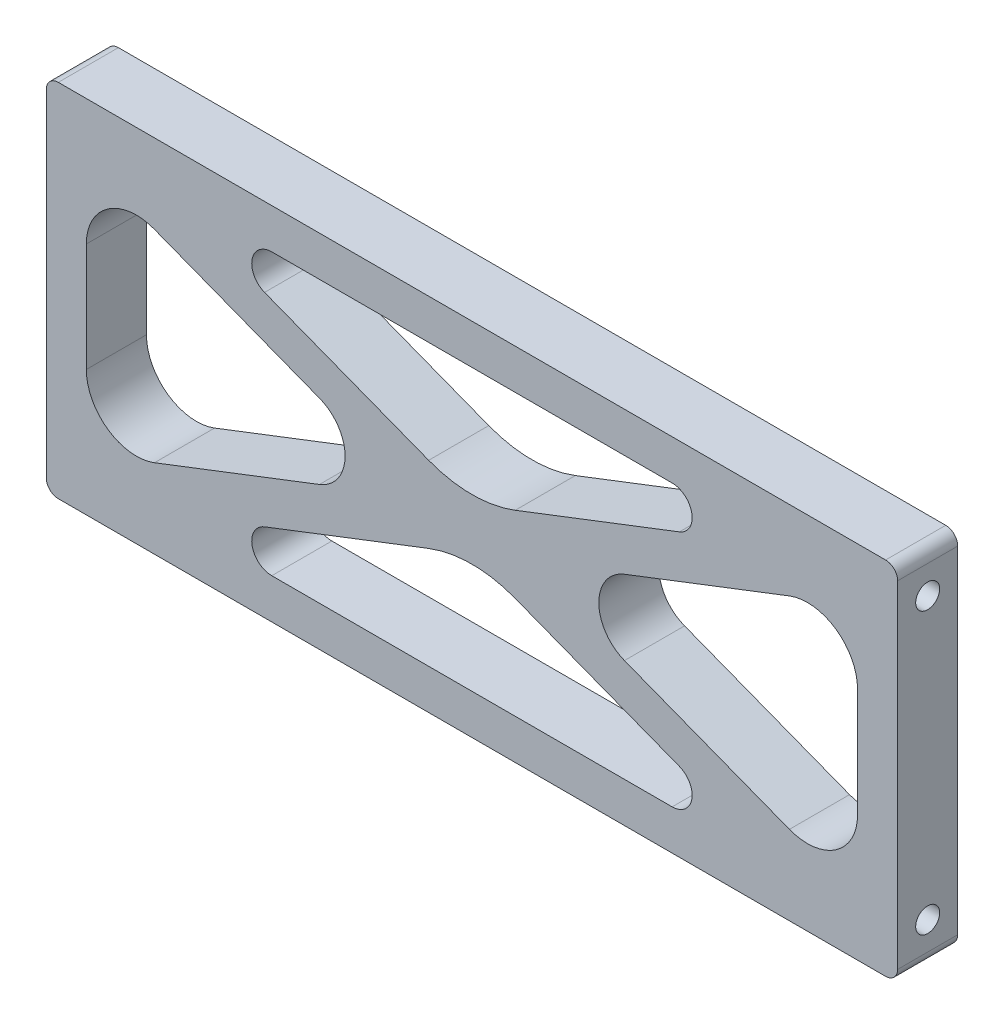
SolidWorks part; units mm, degrees
material "6061-T6 (SS)"
ref_plane "Front" through (0, 0, 0) normal (0, 0, 1) x (1, 0, 0)
ref_plane "Top" through (0, 0, 0) normal (0, 1, 0) x (1, 0, 0)
ref_plane "Right" through (0, 0, 0) normal (1, 0, 0) x (0, 0, -1)
sketch "Sketch1" plane through (0, 0, 0) normal (0, 0, 1) x (1, 0, 0)
  line L1 (-67.4624, 28.575) -> (67.4624, 28.575)
  line L2 (-67.4624, 28.575) -> (-67.4624, -28.575)
  line L3 (-67.4624, -28.575) -> (67.4624, -28.575)
  line L4 (67.4624, 28.575) -> (67.4624, -28.575)
  line L5 (-67.4624, 28.575) -> (67.4624, -28.575) construction
  line L6 (-67.4624, -28.575) -> (67.4624, 28.575) construction
  line L7 (67.4624, -22.225) -> (-67.4624, -22.225) construction
  line L8 (67.4624, -22.225) -> (67.4624, 22.225) construction
  line L9 (67.4624, 22.225) -> (-67.4624, 22.225) construction
  line L10 (-67.4624, -22.225) -> (-67.4624, 22.225) construction
  line L11 (67.4624, -22.225) -> (-67.4624, 22.225) construction
  line L12 (67.4624, 22.225) -> (-67.4624, -22.225) construction
  point P0 (0, 0)
  point P6 (0, 0)
  dimension "D1" = 134.9248
  dimension "D2" = 57.15
  dimension "D3" = 44.45
extrude "Boss-Extrude1" add sketch "Sketch1" along normal mid plane 9.525
sketch "Sketch3" plane through (0, 0, 4.7625) normal (0, 0, 1) x (1, 0, 0)
  line L0 (67.4624, -26.035) -> (-67.4624, 26.035) construction
  line L1 (67.4624, 26.035) -> (-67.4624, -26.035) construction
  line L2 (-61.1124, 8.6099) -> (-61.1124, -8.6099)
  line L3 (-50.3171, -16.0151) -> (-24.1693, -5.9242)
  line L4 (-24.1693, 5.9242) -> (-50.3171, 16.0151)
  line L5 (-31.7257, -22.225) -> (31.7257, -22.225)
  line L6 (32.8688, -16.0879) -> (6.8587, -6.0501)
  line L7 (-6.8587, -6.0501) -> (-32.8688, -16.0879)
  line L8 (-67.4624, 0) -> (67.4624, 0) construction
  line L9 (-67.4624, 28.575) -> (-67.4624, -28.575) construction
  line L10 (67.4624, -28.575) -> (67.4624, 28.575) construction
  line L11 (0, 28.575) -> (0, -28.575) construction
  line L12 (67.4624, 28.575) -> (-67.4624, 28.575) construction
  line L13 (-67.4624, -28.575) -> (67.4624, -28.575) construction
  line L14 (-31.7257, 22.225) -> (31.7257, 22.225)
  line L15 (32.8688, 16.0879) -> (6.8587, 6.0501)
  line L16 (-6.8587, 6.0501) -> (-32.8688, 16.0879)
  line L17 (61.1124, 8.6099) -> (61.1124, -8.6099)
  line L18 (50.3171, -16.0151) -> (24.1693, -5.9242)
  line L19 (24.1693, 5.9242) -> (50.3171, 16.0151)
  arc A0 (-24.1693, -5.9242) -> (-24.1693, 5.9242) centre (-26.4555, 0) ccw
  arc A1 (-61.1124, -8.6099) -> (-50.3171, -16.0151) centre (-53.1749, -8.6099) ccw
  arc A2 (-61.1124, 8.6099) -> (-50.3171, 16.0151) centre (-53.1749, 8.6099) cw
  arc A3 (31.7257, -22.225) -> (32.8688, -16.0879) centre (31.7257, -19.05) ccw
  arc A4 (-31.7257, -22.225) -> (-32.8688, -16.0879) centre (-31.7257, -19.05) cw
  arc A5 (6.8587, -6.0501) -> (-6.8587, -6.0501) centre (0, -23.8226) ccw
  arc A6 (31.7257, 22.225) -> (32.8688, 16.0879) centre (31.7257, 19.05) cw
  arc A7 (6.8587, 6.0501) -> (-6.8587, 6.0501) centre (0, 23.8226) cw
  arc A8 (-31.7257, 22.225) -> (-32.8688, 16.0879) centre (-31.7257, 19.05) ccw
  arc A9 (61.1124, -8.6099) -> (50.3171, -16.0151) centre (53.1749, -8.6099) cw
  arc A10 (24.1693, -5.9242) -> (24.1693, 5.9242) centre (26.4555, 0) cw
  arc A11 (61.1124, 8.6099) -> (50.3171, 16.0151) centre (53.1749, 8.6099) ccw
  point P22 (-8.8185, 0)
  point P39 (0, -3.4032)
  point P40 (0, 3.4032)
  point P55 (8.8185, 0)
  dimension "D3" = 6.35
  dimension "D6" = 3.175
  dimension "D7" = 19.05
  dimension "D8" = 7.9375
  dimension "D1" = 6.35
  dimension "D2" = 3.175
  dimension "D4" = 3.175
  dimension "D5" = 6.35
  dimension "D9" = 2.54
  dimension "D10" = 2.54
  dimension "D11" = 2.54
  dimension "D12" = 2.54
extrude "Cut-Extrude1" cut sketch "Sketch3" against normal through all
hole_wizard "#10-24 Tapped Hole1" positions "Sketch5" profile "Sketch4" tap size "#10-24" standard "Ansi Inch"
sketch "Sketch5" plane through (-67.4624, 0, 0) normal (-1, 0, 0) x (0, 0, 1)
  line L0 (0, 22.225) -> (0, -22.225) construction
  point P0 (0, 22.225)
  point P1 (0, -22.225)
  dimension "D1" = 44.45
sketch "Sketch4" plane through (-67.4624, 22.225, 0) normal (0, 1, 0) x (0, 0, 1)
  line L0 (0, 0) -> (0, 14.0948)
  line L1 (0, 14.0948) -> (1.8986, 12.954)
  line L2 (1.8986, 12.954) -> (1.8986, 0)
  line L5 (1.8986, 0) -> (0, 0)
  line L10 (0, 14.0948) -> (-1.8987, 12.954) construction
  line L11 (0, -6.35) -> (0, 107.95) construction
  dimension "Tap Drill Dia." = 3.7973
  dimension "Tap Drill Depth" = 12.954
  dimension "Drill Angle" = 118
cosmetic thread "Hole Thread1" parameters "D1"=9.652, "D2"=4.826
cosmetic thread "Hole Thread2" parameters "D1"=9.652, "D2"=4.826
mirror "Mirror1" about plane through (0, 0, 0) normal (1, 0, 0) of "#10-24 Tapped Hole1"
fillet "Fillet1" radius 1.905 4 edges at (67.4624, 28.575, 0) (67.4624, -28.575, 0) (-67.4624, -28.575, 0) (-67.4624, 28.575, 0)
